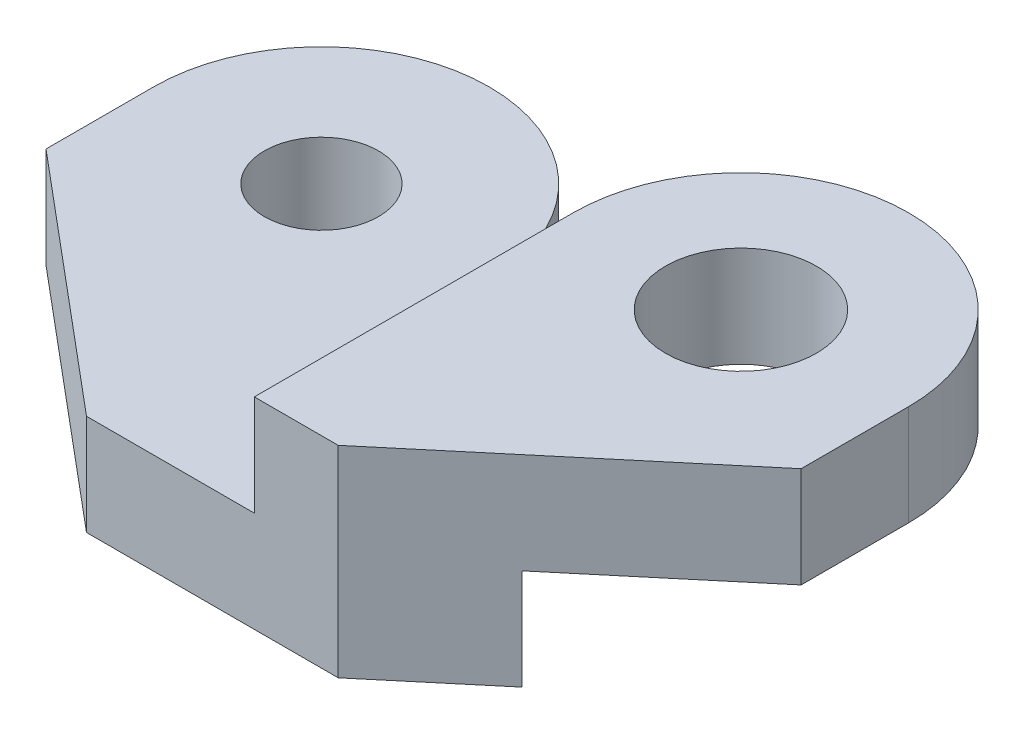
SolidWorks part; units mm, degrees
ref_plane "Plan de face" through (0, 0, 0) normal (0, 0, 1) x (1, 0, 0)
ref_plane "Plan de dessus" through (0, 0, 0) normal (0, 1, 0) x (1, 0, 0)
ref_plane "Plan de droite" through (0, 0, 0) normal (1, 0, 0) x (0, 0, -1)
sketch "Esquisse1" plane through (0, 0, 0) normal (0, 1, 0) x (1, 0, 0)
  line L0 (0, 0) -> (0, 30)
  line L1 (20, 30) -> (20, 0)
  arc A0 (20, 30) -> (0, 30) centre (10, 30) ccw
  arc A1 (0, 0) -> (20, 0) centre (10, 0) ccw
  dimension "D1" = 20
  dimension "D2" = 30
extrude "Boss.-Extru.1" add sketch "Esquisse1" along normal blind 6
sketch "Esquisse7" plane through (0, 6, 0) normal (0, 1, 0) x (1, 0, 0)
  arc A0 (20, 30) -> (0, 30) centre (10, 30) ccw construction
  arc A1 (0, 0) -> (20, 0) centre (10, 0) ccw construction
  point P0 (10, 30)
  point P5 (10, 0)
sketch "Esquisse12" plane through (0, 0, 0) normal (0, -1, 0) x (1, 0, 0)
  line L0 (0, -30) -> (20, -30)
  line L1 (0, -30) -> (0, 0) construction
  line L2 (20, 0) -> (20, -30) construction
  line L3 (20, -30) -> (20, 0)
  line L4 (0, 0) -> (0, -30)
  arc A0 (20, 0) -> (0, 0) centre (10, 0) ccw construction
  arc A1 (20, 0) -> (0, 0) centre (10, 0) ccw
extrude "Boss.-Extru.2" add sketch "Esquisse12" along normal blind 12
sketch "Esquisse14" plane through (20, 0, 0) normal (1, 0, 0) x (0, 0, -1)
  line L0 (11, 6) -> (11, 0)
  line L1 (0, 6) -> (30, 6) construction
  line L2 (11, 0) -> (-10, 0)
  line L3 (-10, 6) -> (-10, -12) construction
  line L4 (-10, 0) -> (-10, 6)
  line L5 (-10, 6) -> (11, 6)
  line L6 (30, 0) -> (40, 0) construction
  line L7 (15, 10.1399) -> (15, -19.2589) construction
  line L10 (0, 6) -> (0, -12) construction
  line L11 (30, 6) -> (30, 0) construction
  line L12 (30, 0) -> (19, 0)
  line L13 (19, 0) -> (19, -6)
  line L14 (19, -6) -> (-10, -6)
  line L15 (-10, -6) -> (-10, -12)
  line L16 (-10, -12) -> (0, -12) construction
  line L17 (-10, -12) -> (30, -12)
  line L18 (30, -12) -> (30, 0)
  dimension "D1" = 4
  dimension "D2" = 6
  dimension "D3" = 8
extrude "Enlèv. mat.-Extru.2" cut sketch "Esquisse14" against normal through all
hole_wizard "Dégagement M81" positions "Esquisse15" profile "Esquisse16" hole size "M8" standard "ISO" end condition through all
sketch "Esquisse15" plane through (0, 6, 0) normal (0, 1, 0) x (1, 0, 0)
  point P0 (10, 30)
sketch "Esquisse16" plane through (10, 6, -30) normal (1, 0, 0) x (0, 0, 1)
  line L0 (0, 0) -> (0, 12)
  line L1 (0, 12) -> (4.5, 12)
  line L2 (4.5, 12) -> (4.5, 0)
  line L5 (4.5, 0) -> (0, 0)
  line L11 (0, -6.35) -> (0, 107.95) construction
  dimension "Diamètre du perçage jusqu'au prochain" = 9
  dimension "Profondeur du perçage jusqu'au prochain" = 12
hole_wizard "Trou taraudé M82" positions "Esquisse17" profile "Esquisse18" tap size "M8" standard "ISO" end condition through all
sketch "Esquisse17" plane through (0, 0, 0) normal (0, 1, 0) x (1, 0, 0)
  arc A0 (0, 0) -> (20, 0) centre (10, 0) ccw construction
  point P0 (10, 0)
cosmetic thread "Filetage de perçage13" parameters "D2"=8
sketch "Esquisse18" plane through (10, 0, 0) normal (1, 0, 0) x (0, 0, 1)
  line L0 (0, 0) -> (0, 6)
  line L1 (0, 6) -> (3.4, 6)
  line L2 (3.4, 6) -> (3.4, 0)
  line L5 (3.4, 0) -> (0, 0)
  line L11 (0, -6.35) -> (0, 107.95) construction
  dimension "Diamètre du trou pour taraudage jusqu'au prochain" = 6.8
  dimension "Profondeur du trou pour taraudage jusqu'au prochain" = 6
sketch "Esquisse19" plane through (0, 0, -11) normal (0, 0, 1) x (1, 0, 0)
  line L1 (-6.919, -8.7193) -> (24.3091, -8.7193)
  line L2 (-6.919, -8.7193) -> (-6.919, 7.314)
  line L3 (-6.919, 7.314) -> (24.3091, 7.314)
  line L4 (24.3091, -8.7193) -> (24.3091, 7.314)
extrude "Enlèv. mat.-Extru.3" cut sketch "Esquisse19" along normal through all
sketch "Esquisse20" plane through (0, 0, 0) normal (-1, 0, 0) x (0, 0, 1)
  line L1 (-19, 0) -> (-11, 0)
  line L2 (-19, 0) -> (-19, -6)
  line L3 (-19, -6) -> (-11, -6)
  line L4 (-11, 0) -> (-11, -6)
extrude "Boss.-Extru.3" add sketch "Esquisse20" along normal blind 25
sketch "Esquisse21" plane through (0, -6, 0) normal (0, -1, 0) x (1, 0, 0)
  line L0 (-25, -19) -> (-25, -30)
  line L1 (-25, -19) -> (-5, -19)
  line L3 (-5, -19) -> (-5, -30)
  arc A0 (-25, -30) -> (-5, -30) centre (-15, -30) ccw
  dimension "D1" = 20
  dimension "D2" = 11
  dimension "D3" = 11
extrude "Boss.-Extru.4" add sketch "Esquisse21" against normal blind 6
hole_wizard "Trou taraudé M83" positions "Esquisse22" profile "Esquisse24" tap size "M8" standard "ISO" end condition through all
sketch "Esquisse22" plane through (0, 0, 0) normal (0, 1, 0) x (1, 0, 0)
  arc A0 (-5, 30) -> (-25, 30) centre (-15, 30) ccw construction
  point P0 (-15, 30)
sketch "Esquisse24" plane through (-15, 0, -30) normal (1, 0, 0) x (0, 0, 1)
  line L0 (0, 0) -> (0, 6)
  line L1 (0, 6) -> (3.4, 6)
  line L2 (3.4, 6) -> (3.4, 0)
  line L5 (3.4, 0) -> (0, 0)
  line L11 (0, -6.35) -> (0, 107.95) construction
  dimension "Diamètre du trou pour taraudage jusqu'au prochain" = 6.8
  dimension "Profondeur du trou pour taraudage jusqu'au prochain" = 6
cosmetic thread "Filetage de perçage14" parameters "D2"=8
sketch "Esquisse25" plane through (0, 0, -19) normal (0, 0, -1) x (-1, 0, 0)
  line L1 (5, 0) -> (-20, 0)
  line L2 (5, 0) -> (5, -6)
  line L3 (5, -6) -> (-20, -6)
  line L4 (-20, 0) -> (-20, -6)
extrude "Enlèv. mat.-Extru.4" cut sketch "Esquisse25" against normal blind 3
ref_plane "Plan1" through (-2.5, 0, 0) normal (1, 0, 0) x (0, 0, -1)
sketch "Esquisse27" plane through (0, -6, 0) normal (0, -1, 0) x (1, 0, 0)
  line L0 (-25, -11) -> (-10, -11)
  line L5 (20, -11) -> (-25, -11) construction
  line L6 (-10, -11) -> (-25, -23.5865)
  line L7 (-25, -30) -> (-25, -11) construction
  line L8 (-25, -23.5865) -> (-25, -11)
  dimension "D1" = 50
  dimension "D2" = 15
extrude "Enlèv. mat.-Extru.5" cut sketch "Esquisse27" against normal through all both and the other way through all
mirror "Symétrie1" about plane through (-2.5, 0, 0) normal (1, 0, 0) of "Enlèv. mat.-Extru.5"
sketch "Esquisse28" plane through (0, 0, 0) normal (-1, 0, 0) x (0, 0, 1)
  line L1 (-11, 6) -> (-16, 6)
  line L2 (-11, 6) -> (-11, 0)
  line L3 (-11, 0) -> (-16, 0)
  line L4 (-16, 6) -> (-16, 0)
